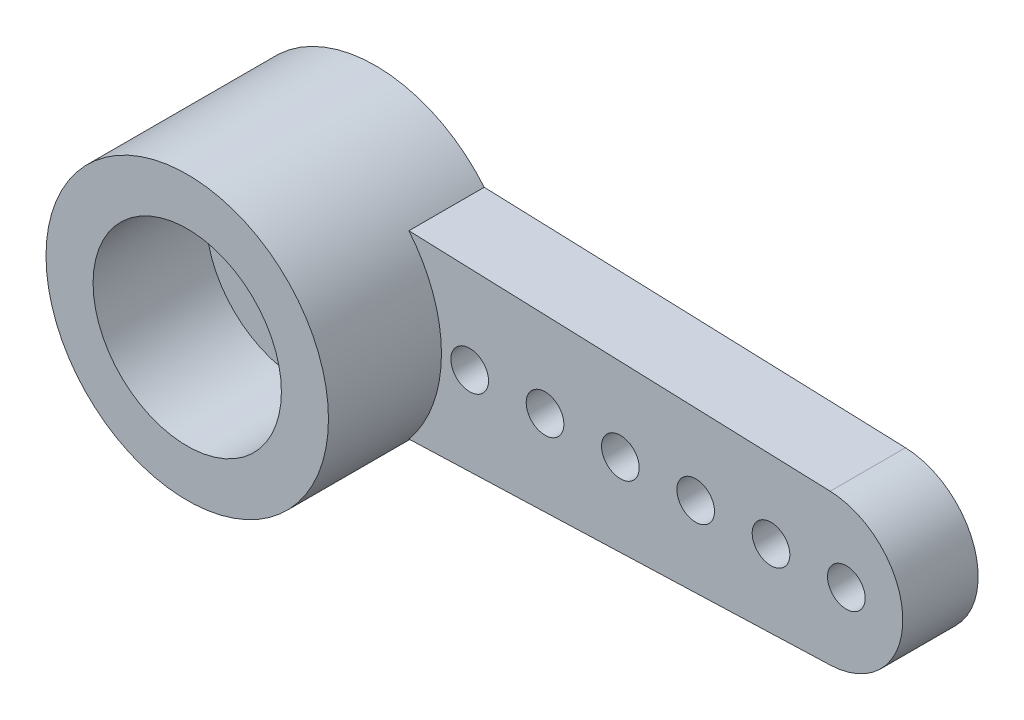
SolidWorks part; units mm, degrees
ref_plane "Спереди" through (0, 0, 0) normal (0, 0, 1) x (1, 0, 0)
ref_plane "Сверху" through (0, 0, 0) normal (0, 1, 0) x (1, 0, 0)
ref_plane "Справа" through (0, 0, 0) normal (1, 0, 0) x (0, 0, -1)
sketch "Эскиз1" plane through (0, 0, 0) normal (0, 0, 1) x (1, 0, 0)
  line L0 (0, 0) -> (-14, 0)
  line L1 (-2.8855, 2.3951) -> (0, 2.4974)
  line L2 (-2.8855, -2.3951) -> (0, -2.4974)
  line L4 (14.0708, -1.9987) -> (0, -2.4974)
  line L5 (14.0708, 1.9987) -> (0, 2.4974)
  circle A0 centre (0, 0) radius 3.75
  circle A1 centre (0, 0) radius 2.5
  arc A3 (13.967, -1.9997) -> (14.0708, 1.9987) centre (14, 0) ccw
  dimension "D1" = 7.5
  dimension "D2" = 5
  dimension "D3" = 14
extrude "Бобышка-Вытянуть3" add sketch "Эскиз1" along normal blind 2
sketch "Эскиз2" plane through (0, 0, 2) normal (0, 0, 1) x (1, 0, 0)
  circle A0 centre (0, 0) radius 3.75
  circle A1 centre (0, 0) radius 2.5
  dimension "D1" = 5
extrude "Бобышка-Вытянуть5" add sketch "Эскиз2" along normal blind 3 separate body
sketch "Эскиз3" plane through (0, 0, 2) normal (0, 0, -1) x (-1, 0, 0)
  circle A0 centre (0, 0) radius 3.75
  circle A1 centre (0, 0) radius 2.5
  circle A2 centre (0, 0) radius 3.75 construction
  dimension "D1" = 5
  dimension "D2" = 7.5
extrude "Бобышка-Вытянуть6" add sketch "Эскиз3" along normal blind 2
sketch "Эскиз4" plane through (0, 0, 0) normal (0, 0, -1) x (-1, 0, 0)
  line L0 (-16, 0) -> (-14.5, 0)
  line L1 (-14.5, 0) -> (-12.5, 0)
  line L2 (-12.5, 0) -> (-10.5, 0)
  line L3 (-10.5, 0) -> (-8.5, 0)
  line L4 (-8.5, 0) -> (-6.5, 0)
  line L5 (-6.5, 0) -> (-4.5, 0)
  arc A0 (-14.0708, 1.9987) -> (-14.0708, -1.9987) centre (-14, 0) ccw construction
  circle A1 centre (-14.5, 0) radius 0.5
  circle A2 centre (-12.5, 0) radius 0.5
  circle A3 centre (-10.5, 0) radius 0.5
  circle A4 centre (-8.5, 0) radius 0.5
  circle A5 centre (-6.5, 0) radius 0.5
  circle A6 centre (-4.5, 0) radius 0.5
  circle A7 centre (4.5, 0) radius 0.5
  circle A8 centre (6.5, 0) radius 0.5
  circle A9 centre (8.5, 0) radius 0.5
  circle A10 centre (10.5, 0) radius 0.5
  circle A11 centre (12.5, 0) radius 0.5
  circle A12 centre (14.5, 0) radius 0.5
  dimension "D2" = 1
  dimension "D8" = 1
  dimension "D9" = 1
  dimension "D10" = 1
  dimension "D11" = 1
  dimension "D12" = 1
  dimension "D1" = 1.5
  dimension "D3" = 2
  dimension "D4" = 2
  dimension "D5" = 2
  dimension "D6" = 2
  dimension "D7" = 2
extrude "Вырез-Вытянуть1" cut sketch "Эскиз4" against normal blind 2
sketch "Эскиз5" plane through (0, 0, 0) normal (0, 0, -1) x (-1, 0, 0)
  circle A0 centre (0, 0) radius 2.5
extrude "Бобышка-Вытянуть7" add sketch "Эскиз5" against normal blind 1
sketch "Эскиз6" plane through (0, 0, 0) normal (0, 0, -1) x (-1, 0, 0)
  circle A0 centre (0, 0) radius 2.5
  dimension "D1" = 5
extrude "Вырез-Вытянуть2" cut sketch "Эскиз6" against normal blind 0.5
sketch "Эскиз7" plane through (0, 0, 0.5) normal (0, 0, -1) x (-1, 0, 0)
  circle A0 centre (0, 0) radius 1.25
  dimension "D1" = 2.5
extrude "Вырез-Вытянуть3" cut sketch "Эскиз7" against normal blind 5
sketch "Эскиз8" plane through (0, 0, 0.5) normal (0, 0, -1) x (-1, 0, 0)
  line L0 (-2.8252, -0.1999) -> (-2.8894, -0.2509)
